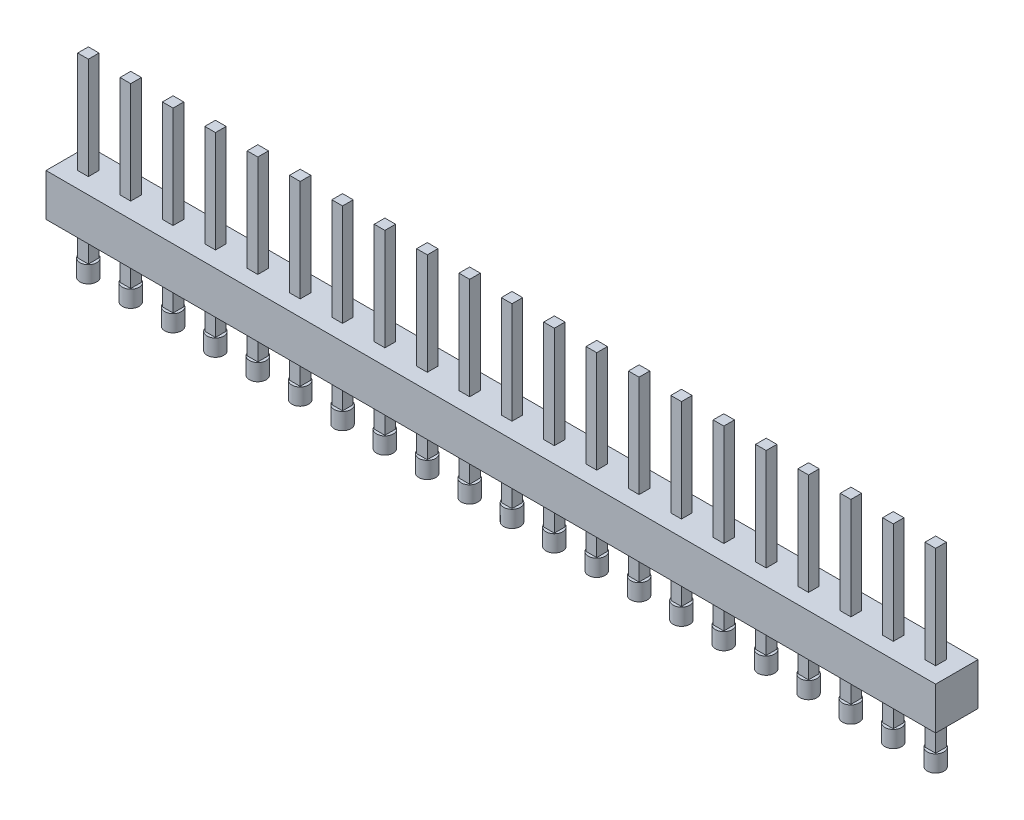
SolidWorks part; units mm, degrees
ref_plane "Front Plane" through (0, 0, 0) normal (0, 0, 1) x (1, 0, 0)
ref_plane "Top Plane" through (0, 0, 0) normal (0, 1, 0) x (1, 0, 0)
ref_plane "Right Plane" through (0, 0, 0) normal (1, 0, 0) x (0, 0, -1)
sketch "Sketch1" plane through (0, 0, 0) normal (0, 1, 0) x (1, 0, 0)
  line L1 (0, 0) -> (2.54, 0)
  line L2 (0, 0) -> (0, 2.54)
  line L3 (0, 2.54) -> (2.54, 2.54)
  line L4 (2.54, 0) -> (2.54, 2.54)
  dimension "D2" = 2.54
extrude "Boss-Extrude1" add sketch "Sketch1" along normal blind 2.54
sketch "Sketch2" plane through (0, 2.54, 0) normal (0, 1, 0) x (1, 0, 0)
  line L0 (1.27, 2.54) -> (1.27, 1.59) construction
  line L1 (0.95, 1.59) -> (1.59, 1.59)
  line L2 (0.95, 1.59) -> (0.95, 0.95)
  line L3 (0.95, 0.95) -> (1.59, 0.95)
  line L4 (1.59, 1.59) -> (1.59, 0.95)
  line L5 (2.54, 2.54) -> (0, 2.54) construction
  line L6 (0, 1.27) -> (0.95, 1.27) construction
  line L7 (0, 2.54) -> (0, 0) construction
  point P12 (0.95, 1.27)
  point P13 (1.27, 1.59)
  dimension "D1" = 0.64
extrude "Boss-Extrude2" add sketch "Sketch2" along normal blind 6.1 and the other way offset from surface (5.54 mm away) 3 other way up to face at (1.27, 0, -1.27)
sketch "Sketch3" plane through (0, -3, 0) normal (0, -1, 0) x (1, 0, 0)
  line L0 (1.27, -0.95) -> (1.27, -1.27) construction
  line L1 (0.95, -0.95) -> (1.59, -0.95) construction
  line L2 (1.27, -1.27) -> (1.59, -1.27) construction
  line L3 (1.59, -0.95) -> (1.59, -1.59) construction
  circle A0 centre (1.27, -1.27) radius 0.5
  dimension "D1" = 1
extrude "Boss-Extrude3" add sketch "Sketch3" against normal blind 1
pattern_linear "LPattern1" count 21 spacing 2.54 along (1, 0, 0) of "Boss-Extrude1", "Boss-Extrude3", "Boss-Extrude2"
